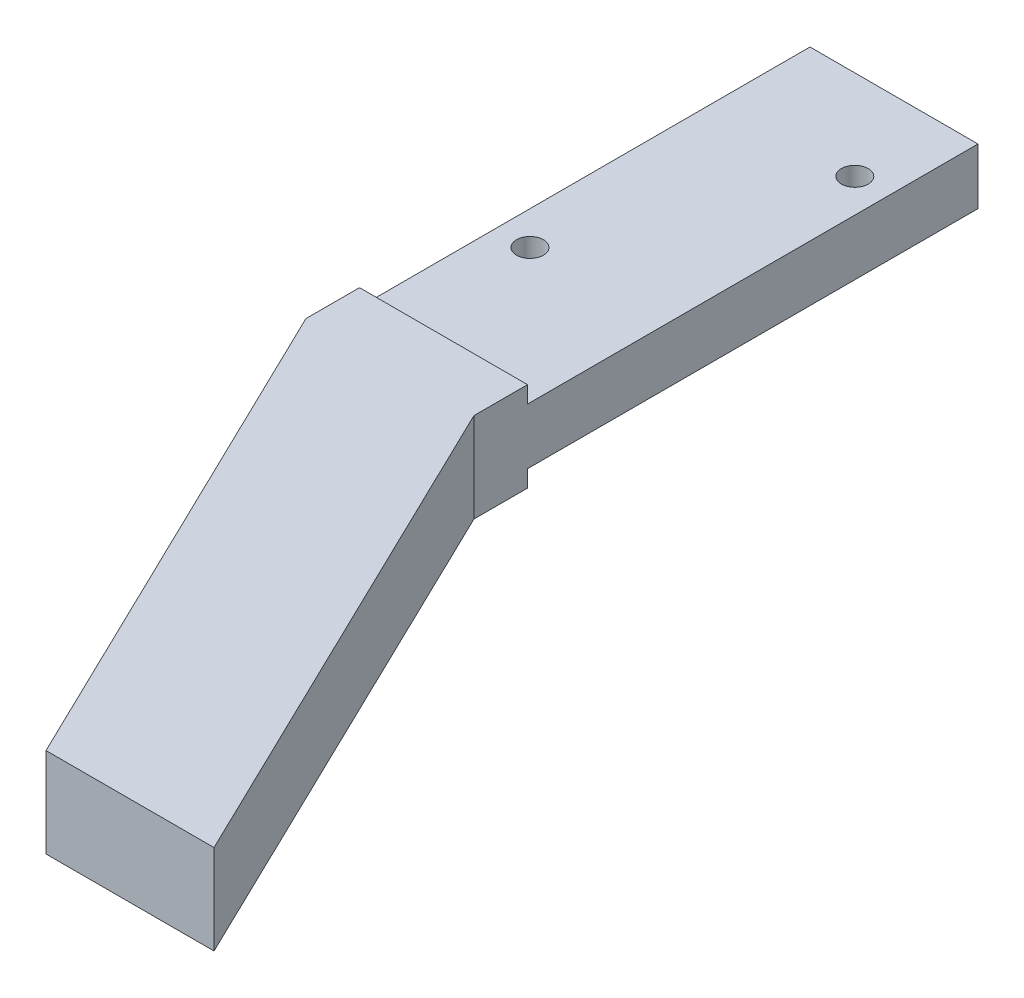
SolidWorks part; units mm, degrees
ref_plane "Front Plane" through (0, 0, 0) normal (0, 0, 1) x (1, 0, 0)
ref_plane "Top Plane" through (0, 0, 0) normal (0, 1, 0) x (1, 0, 0)
ref_plane "Right Plane" through (0, 0, 0) normal (1, 0, 0) x (0, 0, -1)
sketch "Sketch1" plane through (0, 0, 0) normal (0, 1, 0) x (1, 0, 0)
  line L1 (7.5, -22.5) -> (-7.5, -22.5)
  line L2 (7.5, -22.5) -> (7.5, 22.5)
  line L3 (7.5, 22.5) -> (-7.5, 22.5)
  line L4 (-7.5, -22.5) -> (-7.5, 22.5)
  line L5 (7.5, -22.5) -> (-7.5, 22.5) construction
  line L6 (7.5, 22.5) -> (-7.5, -22.5) construction
  circle A0 centre (-4.5, -5.5) radius 1.2
  circle A2 centre (4.5, 14.5) radius 1.2
  point P0 (0, 0)
  dimension "D3" = 28
  dimension "D4" = 3
  dimension "D5" = 2.4
  dimension "D6" = 2.4
  dimension "D1" = 15
  dimension "D2" = 45
  dimension "D7" = 8
  dimension "D8" = 3
extrude "Boss-Extrude1" add sketch "Sketch1" along normal mid plane 5
sketch "Sketch4" plane through (0, 0, 0) normal (0, 1, 0) x (1, 0, 0)
  line L0 (-7.5, -17.7157) -> (-7.5, -22.5)
  line L1 (-7.5, 22.5) -> (-7.5, -22.5) construction
  line L2 (-7.5, -22.5) -> (14.2945, -67.5)
  line L3 (14.2945, -67.5) -> (29.2945, -67.5)
  line L4 (29.2945, -67.5) -> (7.5, -22.5)
  line L5 (-7.5, -17.7157) -> (7.5, -17.7157)
  line L6 (7.5, -22.5) -> (7.5, 22.5) construction
  line L7 (7.5, -17.7157) -> (7.5, -22.5)
  dimension "D1" = 45
  dimension "D2" = 50
extrude "Boss-Extrude2" add sketch "Sketch4" against normal mid plane 8
